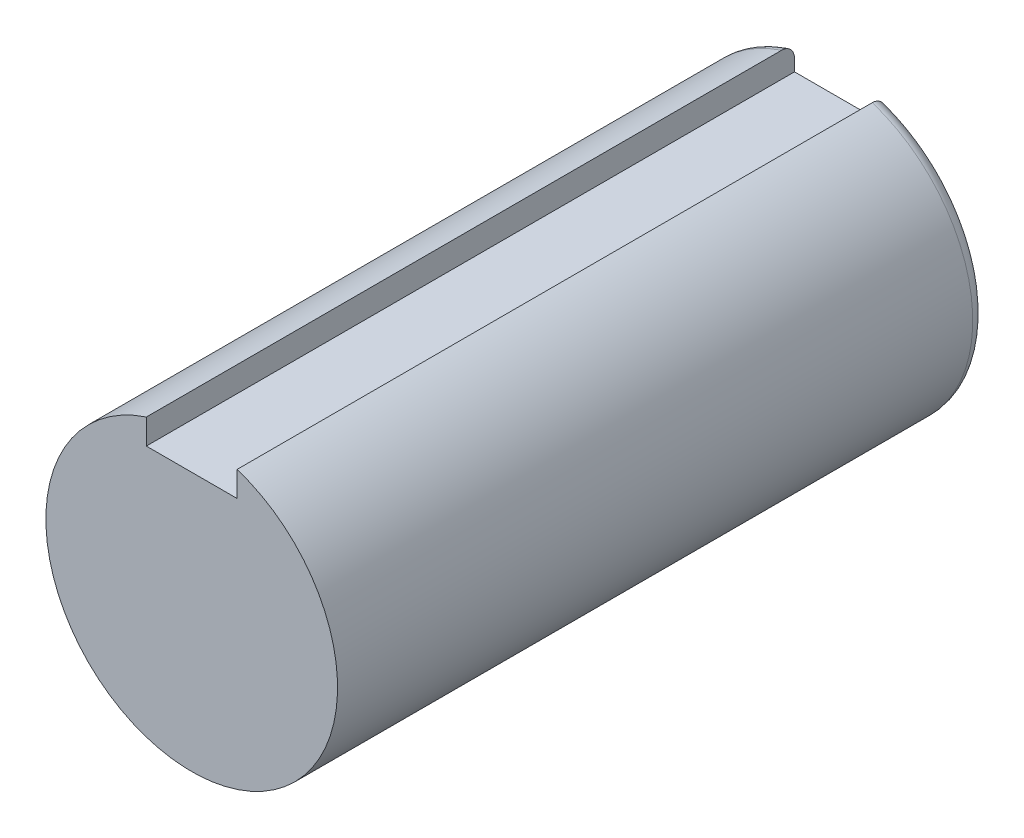
SolidWorks part; units mm, degrees
ref_plane "Front Plane" through (0, 0, 0) normal (0, 0, 1) x (1, 0, 0)
ref_plane "Top Plane" through (0, 0, 0) normal (0, 1, 0) x (1, 0, 0)
ref_plane "Right Plane" through (0, 0, 0) normal (1, 0, 0) x (0, 0, -1)
sketch "Sketch1" plane through (0, 0, 0) normal (0, 0, 1) x (1, 0, 0)
  circle A0 centre (0, 0) radius 22.5
  dimension "D1" = 45
extrude "Boss-Extrude3" add sketch "Sketch1" along normal blind 100
sketch "Sketch5" plane through (0, 0, 0) normal (0, 0, -1) x (-1, 0, 0)
  line L0 (0, 17.5) -> (0, 0) construction
  line L1 (-7, 25.301) -> (7, 25.301)
  line L2 (-7, 25.301) -> (-7, 17.5)
  line L3 (-7, 17.5) -> (7, 17.5)
  line L4 (7, 25.301) -> (7, 17.5)
  point P4 (0, 17.5)
  dimension "D1" = 14
  dimension "D2" = 17.5
extrude "Cut-Extrude2" cut sketch "Sketch5" against normal blind 100
fillet "Fillet1" radius 2 1 edges at (0, -22.5, 0)
